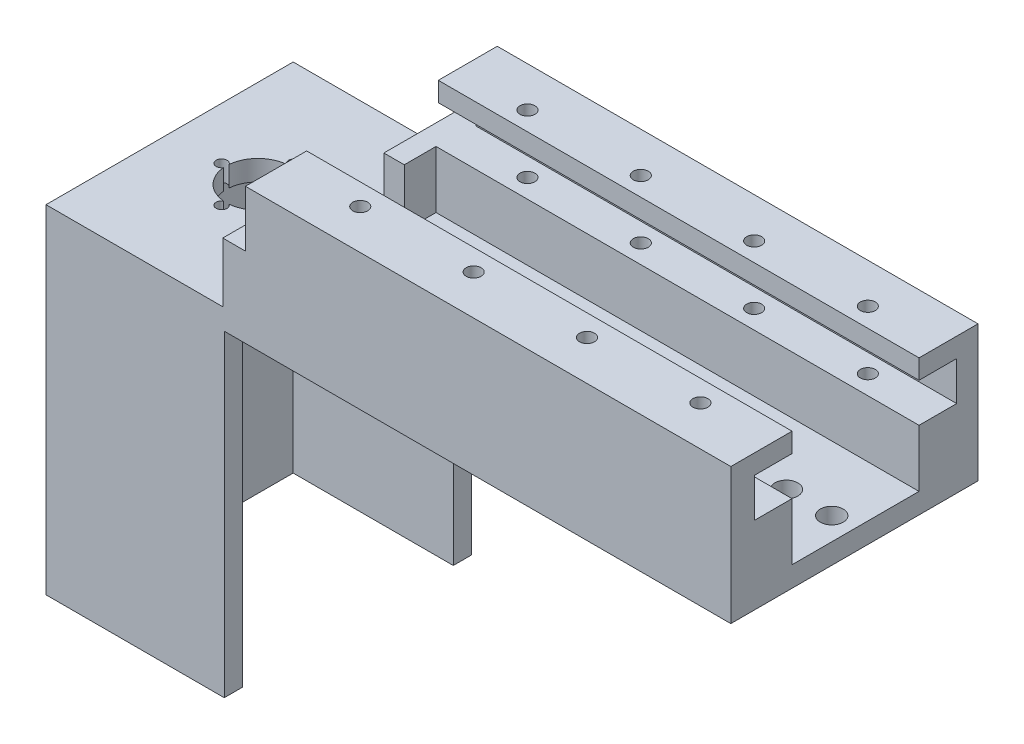
SolidWorks part; units mm, degrees
ref_plane "Front Plane" through (0, 0, 0) normal (0, 0, 1) x (1, 0, 0)
ref_plane "Top Plane" through (0, 0, 0) normal (0, 1, 0) x (1, 0, 0)
ref_plane "Right Plane" through (0, 0, 0) normal (1, 0, 0) x (0, 0, -1)
sketch "Sketch4" plane through (0, 0, 0) normal (0, 0, 1) x (1, 0, 0)
  line L1 (-89.891, -20.3228) -> (16.109, -20.3228)
  line L2 (-89.891, -20.3228) -> (-89.891, -50.3228)
  line L3 (-89.891, -50.3228) -> (16.109, -50.3228)
  line L4 (16.109, -20.3228) -> (16.109, -50.3228)
  dimension "D1" = 30
  dimension "D2" = 106
extrude "Boss-Extrude2" add sketch "Sketch4" against normal blind 13
sketch "Sketch25" plane through (0, 0, 0) normal (0, 0, 1) x (1, 0, 0)
  line L0 (-89.891, -20.3228) -> (-89.891, -50.3228) construction
  line L1 (-89.891, -24.6013) -> (16.109, -24.6013)
  line L2 (-89.891, -24.6013) -> (-89.891, -33.2013)
  line L3 (-89.891, -33.2013) -> (16.109, -33.2013)
  line L4 (16.109, -24.6013) -> (16.109, -33.2013)
  line L5 (16.109, -50.3228) -> (16.109, -20.3228) construction
  dimension "D1" = 8.6
extrude "Cut-Extrude3" cut sketch "Sketch25" against normal blind 8.3 and the other way through all
hole_wizard "M4x0.7 Tapped Hole1" positions "3DSketch1" profile "Sketch27" tap size "M4x0.7" standard "ANSI Metric" end condition through all
sketch3d "3DSketch1"
  line L0 (16.109, -20.3228, -13) -> (16.109, -20.3228, 0) construction
  line L2 (16.109, -20.3228, 0) -> (-89.891, -20.3228, 0) construction
  line L3 (-89.891, -20.3228, -13) -> (-89.891, -20.3228, 0) construction
  point P0 (-74.391, -20.3228, -4.15)
  point P2 (-49.391, -20.3228, -4.15)
  point P4 (0.609, -20.3228, -4.2057)
  point P6 (-24.391, -20.3228, -4.15)
  dimension "D1" = 15.5
  dimension "D2" = 25
  dimension "D5" = 4.15
  dimension "D6" = 4.15
  dimension "D7" = 4.15
  dimension "D8" = 25
  dimension "D9" = 25
  dimension "D10" = 15.5001
cosmetic thread "Hole Thread2" parameters "D1"=8, "D2"=4
cosmetic thread "Hole Thread3" parameters "D1"=8, "D2"=4
cosmetic thread "Hole Thread4" parameters "D1"=8, "D2"=4
cosmetic thread "Hole Thread5" parameters "D1"=8, "D2"=4
sketch "Sketch27" plane through (-74.391, -20.3228, -4.15) normal (1, 0, 0) x (0, 0, 1)
  line L0 (0, 0) -> (0, 30)
  line L1 (0, 30) -> (1.65, 30)
  line L2 (1.65, 30) -> (1.65, 0)
  line L5 (1.65, 0) -> (0, 0)
  line L11 (0, -6.35) -> (0, 107.95) construction
  dimension "Thru Tap Drill Dia." = 3.3
  dimension "Thru Tap Drill Depth" = 30
sketch "Sketch28" plane through (0, 0, 0) normal (0, 0, 1) x (1, 0, 0)
  line L0 (-89.891, -33.2013) -> (-89.891, -50.3228) construction
  line L1 (-89.891, -45.8228) -> (16.109, -45.8228)
  line L2 (-89.891, -45.8228) -> (-89.891, -50.3228)
  line L3 (-89.891, -50.3228) -> (16.109, -50.3228)
  line L4 (16.109, -45.8228) -> (16.109, -50.3228)
  dimension "D1" = 4.5
extrude "Boss-Extrude3" add sketch "Sketch28" along normal blind 41.5
sketch "Sketch32" plane through (-89.891, 0, 0) normal (-1, 0, 0) x (0, 0, 1)
  line L1 (0, -45.8228) -> (41.5, -45.8228)
  line L2 (0, -45.8228) -> (0, -50.3228)
  line L3 (0, -50.3228) -> (41.5, -50.3228)
  line L4 (41.5, -45.8228) -> (41.5, -50.3228)
extrude "Boss-Extrude10" add sketch "Sketch32" along normal blind 5
sketch "Sketch33" plane through (-89.891, 0, 0) normal (-1, 0, 0) x (0, 0, 1)
  line L1 (0, -33.2013) -> (-13, -33.2013)
  line L2 (0, -33.2013) -> (0, -50.3228)
  line L3 (0, -50.3228) -> (-13, -50.3228)
  line L4 (-13, -33.2013) -> (-13, -50.3228)
extrude "Boss-Extrude12" add sketch "Sketch33" along normal blind 5
sketch "Sketch34" plane through (0, 0, 0) normal (0, 0, 1) x (1, 0, 0)
  line L0 (16.109, -45.8228) -> (-94.891, -45.8228) construction
  line L1 (-94.891, -33.2013) -> (-90.3922, -33.2013)
  line L2 (-94.891, -33.2013) -> (-94.891, -45.8228)
  line L3 (-94.891, -45.8228) -> (-90.3922, -45.8228)
  line L4 (-90.3922, -33.2013) -> (-90.3922, -45.8228)
extrude "Boss-Extrude13" add sketch "Sketch34" along normal blind 7
sketch "Sketch35" plane through (-94.891, 0, 0) normal (-1, 0, 0) x (0, 0, 1)
  line L1 (41.5, -45.8228) -> (-13, -45.8228)
  line L2 (41.5, -45.8228) -> (41.5, -50.3228)
  line L3 (41.5, -50.3228) -> (-13, -50.3228)
  line L4 (-13, -45.8228) -> (-13, -50.3228)
extrude "Boss-Extrude14" add sketch "Sketch35" along normal blind 40 contours L2 L1 L4 L3
sketch "Sketch36" plane through (0, -45.8228, 0) normal (0, 1, 0) x (1, 0, 0)
  line L0 (16.109, -41.5) -> (-134.891, -41.5) construction
  line L1 (-90.9181, -41.5) -> (-95.9181, -41.5)
  line L2 (-90.9181, -41.5) -> (-90.9181, -21.5)
  line L3 (-90.9181, -21.5) -> (-95.9181, -21.5)
  line L4 (-95.9181, -41.5) -> (-95.9181, -21.5)
  dimension "D1" = 5
  dimension "D2" = 20
extrude "Boss-Extrude15" add sketch "Sketch36" along normal blind 13.12 contours L2 L3 L4 L1
hole_wizard "#8 (0.199) Diameter Hole1" positions "3DSketch3" profile "Sketch38" hole size "#8" standard "Progressive" end condition through all
sketch3d "3DSketch3"
  line L0 (16.109, -45.8228, 41.5) -> (-90.9181, -45.8228, 41.5) construction
  line L1 (16.109, -45.8228, 41.5) -> (16.109, -45.8228, 0) construction
  point P0 (-80.6691, -45.8228, 14.25)
  point P2 (11.109, -45.8228, 14.25)
  point P4 (1.109, -45.8228, 14.25)
  point P6 (-70.6691, -45.8228, 14.25)
  dimension "D1" = 27.25
  dimension "D2" = 27.25
  dimension "D3" = 27.25
  dimension "D4" = 27.25
  dimension "D5" = 10
  dimension "D6" = 10
  dimension "D7" = 5
sketch "Sketch38" plane through (-80.6691, -45.8228, 14.25) normal (1, 0, 0) x (0, 0, 1)
  line L0 (0, 0) -> (0, 4.5)
  line L1 (0, 4.5) -> (2.5273, 4.5)
  line L2 (2.5273, 4.5) -> (2.5273, 0)
  line L5 (2.5273, 0) -> (0, 0)
  line L11 (0, -6.35) -> (0, 107.95) construction
  dimension "Thru Hole Dia." = 5.0546
  dimension "Thru Hole Depth" = 4.5
sketch "Sketch39" plane through (0, -45.8228, 0) normal (0, 1, 0) x (1, 0, 0)
  line L1 (-95.9181, -41.5) -> (-95.9181, -21.5) construction
  line L2 (-134.891, -41.5) -> (-134.891, 13) construction
  line L3 (-134.891, 13) -> (-94.891, 13) construction
  circle A0 centre (-115.4181, -14.25) radius 7
  dimension "D1" = 19.5
  dimension "D2" = 19.4729
  dimension "D3" = 27.25
extrude "Cut-Extrude4" cut sketch "Sketch39" against normal blind 10 contours A0
hole_wizard "M2 Clearance Hole1" positions "3DSketch4" profile "Sketch40" hole size "M2" standard "ANSI Metric" end condition through all
sketch3d "3DSketch4"
  line L0 (-134.891, -45.8228, 41.5) -> (-134.891, -45.8228, -13) construction
  line L1 (-95.9181, -45.8228, 41.5) -> (-134.891, -45.8228, 41.5) construction
  line L3 (-95.9181, -45.8228, 41.5) -> (-95.9181, -45.8228, 21.5) construction
  point P0 (-107.4181, -45.8228, 14.25)
  point P2 (-115.421, -45.8228, 22.25)
  point P4 (-115.421, -45.8228, 6.25)
  point P6 (-123.4181, -45.8228, 14.25)
  point P19 (-115.4046, -45.8228, 41.5)
  dimension "D1" = 19.47
  dimension "D2" = 19.47
  dimension "D3" = 16
  dimension "D4" = 27.25
  dimension "D5" = 27.25
  dimension "D6" = 19.25
  dimension "D7" = 16
  dimension "D8" = 11.5
  dimension "D9" = 11.4729
sketch "Sketch40" plane through (-107.4181, -45.8228, 14.25) normal (1, 0, 0) x (0, 0, 1)
  line L0 (0, 0) -> (0, 4.5)
  line L1 (0, 4.5) -> (1.2, 4.5)
  line L2 (1.2, 4.5) -> (1.2, 0)
  line L5 (1.2, 0) -> (0, 0)
  line L11 (0, -6.35) -> (0, 107.95) construction
  dimension "Thru Hole Dia." = 2.4
  dimension "Thru Hole Depth" = 4.5
sketch "Sketch43" plane through (0, -50.3228, 0) normal (0, -1, 0) x (-1, 0, 0)
  line L0 (134.891, -41.5) -> (-16.109, -41.5) construction
  line L1 (95.5862, -41.5) -> (134.891, -41.5)
  line L2 (95.5862, -41.5) -> (95.5862, -37.5)
  line L3 (95.5862, -37.5) -> (134.891, -37.5)
  line L4 (134.891, -41.5) -> (134.891, -37.5)
  line L5 (134.891, 13) -> (134.891, -41.5) construction
  line L6 (134.891, 13) -> (-16.109, 13) construction
  line L7 (134.891, -37.5) -> (130.891, -37.5)
  line L8 (134.891, -37.5) -> (134.891, 13)
  line L9 (134.891, 13) -> (130.891, 13)
  line L10 (130.891, -37.5) -> (130.891, 13)
  line L12 (95.5862, 13) -> (130.891, 13)
  line L13 (95.5862, 13) -> (95.5862, 9)
  line L14 (95.5862, 9) -> (130.891, 9)
  line L15 (130.891, 13) -> (130.891, 9)
  line M8 (-16.109, -41.5) -> (134.891, -41.5)
  line M9 (134.891, -41.5) -> (134.891, 13)
  line M10 (134.891, 13) -> (-16.109, 13)
  dimension "D1" = 4
  dimension "D2" = 4
  dimension "D3" = 4
extrude "Boss-Extrude16" add sketch "Sketch43" along normal blind 70 contours L3 L2 M8 M9 | L10 L3 M9 M10 | L15 L14 L13 L12
sketch "Sketch44" plane through (0, -45.8228, 0) normal (0, 1, 0) x (1, 0, 0)
  line L0 (16.109, -41.5) -> (16.109, 0) construction
  line L1 (-90.9181, -41.5) -> (16.109, -41.5)
  line L2 (-90.9181, -41.5) -> (-90.9181, -28)
  line L3 (-90.9181, -28) -> (16.109, -28)
  line L4 (16.109, -41.5) -> (16.109, -28)
  dimension "D1" = 13.5
extrude "Boss-Extrude17" add sketch "Sketch44" along normal blind 25.5
sketch "Sketch47" plane through (0, 0, 28) normal (0, 0, -1) x (-1, 0, 0)
  line L0 (-16.109, -20.3228) -> (-16.109, -45.8228) construction
  line L1 (-16.109, -33.2028) -> (90.9181, -33.2028)
  line L2 (-16.109, -33.2028) -> (-16.109, -24.6028)
  line L3 (-16.109, -24.6028) -> (90.9181, -24.6028)
  line L4 (90.9181, -33.2028) -> (90.9181, -24.6028)
  line L5 (90.9181, -20.3228) -> (90.9181, -32.7028) construction
  dimension "D1" = 8.6
  dimension "D2" = 4.28
extrude "Cut-Extrude5" cut sketch "Sketch47" against normal blind 8.3 contours L3 L4 L1 L2
hole_wizard "M4x0.7 Tapped Hole2" positions "3DSketch5" profile "Sketch49" tap size "M4x0.7" standard "ANSI Metric"
sketch3d "3DSketch5"
  line L0 (16.109, -20.3228, 41.5) -> (16.109, -20.3228, 28) construction
  line L1 (-90.9181, -20.3228, 41.5) -> (16.109, -20.3228, 41.5) construction
  point P0 (-74.391, -20.3228, 32.71)
  point P2 (-49.391, -20.3228, 32.71)
  point P4 (-24.391, -20.3228, 32.71)
  point P6 (0.609, -20.3228, 32.71)
  dimension "D1" = 15.5
  dimension "D2" = 8.79
  dimension "D3" = 8.79
  dimension "D4" = 25
  dimension "D5" = 8.79
  dimension "D6" = 25
  dimension "D7" = 25
  dimension "D8" = 8.79
cosmetic thread "Hole Thread6" parameters "D1"=8, "D2"=4
cosmetic thread "Hole Thread7" parameters "D1"=8, "D2"=4
cosmetic thread "Hole Thread8" parameters "D1"=8, "D2"=4
cosmetic thread "Hole Thread9" parameters "D1"=8, "D2"=4
sketch "Sketch49" plane through (-74.391, -20.3228, 32.71) normal (1, 0, 0) x (0, 0, 1)
  line L0 (0, 0) -> (0, 30.9904)
  line L1 (0, 30.9904) -> (1.65, 29.999)
  line L2 (1.65, 29.999) -> (1.65, 0)
  line L5 (1.65, 0) -> (0, 0)
  line L10 (0, 30.9904) -> (-1.65, 29.999) construction
  line L11 (0, -6.35) -> (0, 107.95) construction
  dimension "Tap Drill Dia." = 3.3
  dimension "Tap Drill Depth" = 29.999
  dimension "Drill Angle" = 118
